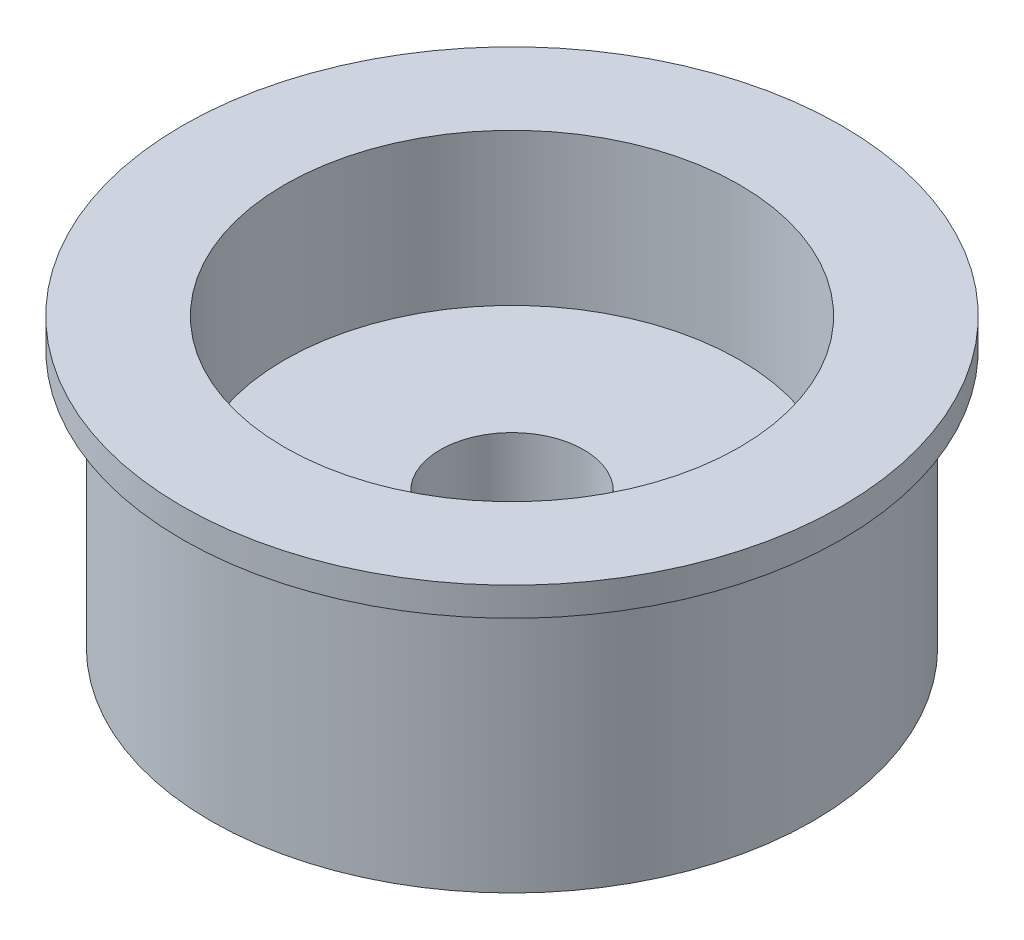
SolidWorks part; units mm, degrees
ref_plane "Front Plane" through (0, 0, 0) normal (0, 0, 1) x (1, 0, 0)
ref_plane "Top Plane" through (0, 0, 0) normal (0, 1, 0) x (1, 0, 0)
ref_plane "Right Plane" through (0, 0, 0) normal (1, 0, 0) x (0, 0, -1)
sketch "Sketch1" plane through (0, 0, 0) normal (0, 1, 0) x (1, 0, 0)
  circle A0 centre (0, 0) radius 14.69
  dimension "D1" = 29.38
extrude "Boss-Extrude1" add sketch "Sketch1" along normal blind 14
sketch "Sketch2" plane through (0, 14, 0) normal (0, 1, 0) x (1, 0, 0)
  circle A0 centre (0, 0) radius 11.1
  dimension "D1" = 22.2
extrude "Cut-Extrude1" cut sketch "Sketch2" against normal blind 7.4
sketch "Sketch3" plane through (0, 14, 0) normal (0, 1, 0) x (1, 0, 0)
  circle A0 centre (0, 0) radius 14.69 construction
  circle A1 centre (0, 0) radius 14.69
  circle A2 centre (0, 0) radius 16.09
  dimension "D1" = 1.4
extrude "Boss-Extrude2" add sketch "Sketch3" against normal blind 1.4
sketch "Sketch4" plane through (0, 6.6, 0) normal (0, 1, 0) x (1, 0, 0)
  circle A0 centre (0, 0) radius 3.5
  dimension "D1" = 7
extrude "Cut-Extrude2" cut sketch "Sketch4" against normal through all
